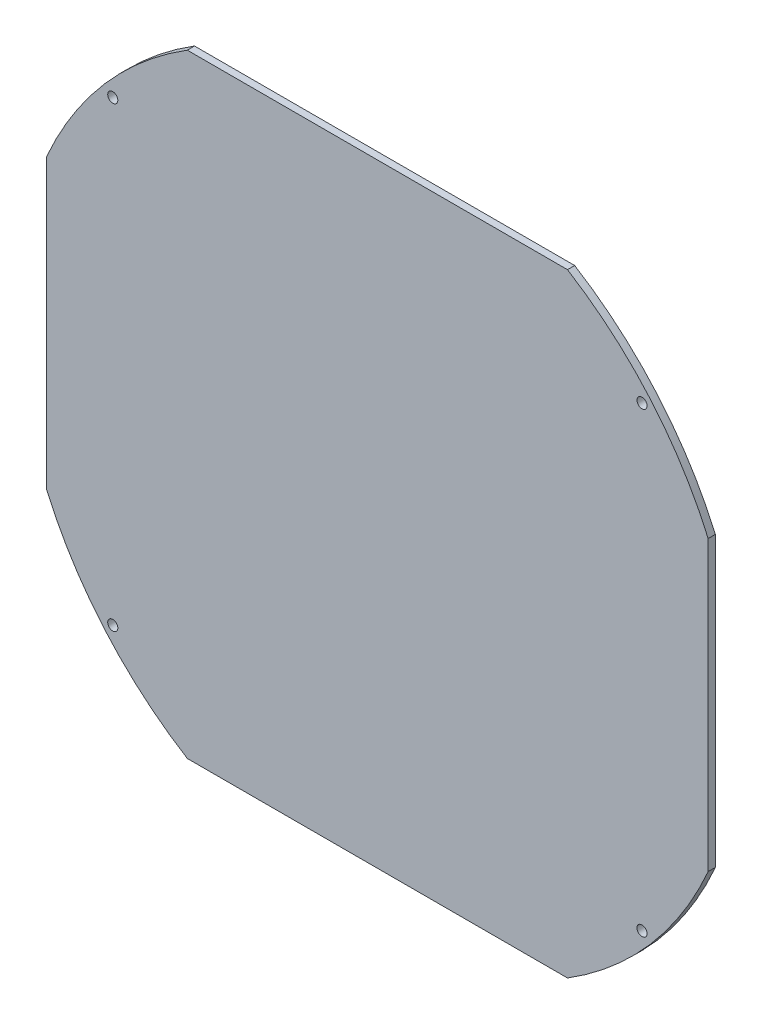
SolidWorks part; units mm, degrees
ref_plane "Front Plane" through (0, 0, 0) normal (0, 0, 1) x (1, 0, 0)
ref_plane "Top Plane" through (0, 0, 0) normal (0, 1, 0) x (1, 0, 0)
ref_plane "Right Plane" through (0, 0, 0) normal (1, 0, 0) x (0, 0, -1)
sketch "Sketch2" plane through (0, 0, 0) normal (0, 0, 1) x (1, 0, 0)
  line L0 (0, 0) -> (0, 125) construction
  line L1 (-57.1063, 125) -> (57.1063, 125)
  line L2 (136.8063, -13.0445) -> (79.7, -111.9555)
  line L3 (0, 0) -> (108.2532, -62.5) construction
  line L4 (-79.7, -111.9555) -> (-136.8063, -13.0445)
  line L5 (0, 0) -> (-108.2532, -62.5) construction
  arc A0 (-79.7, -111.9555) -> (79.7, -111.9555) centre (0, 125) ccw
  arc A1 (-57.1063, 125) -> (-136.8063, -13.0445) centre (108.2532, -62.5) ccw
  arc A2 (136.8063, -13.0445) -> (57.1063, 125) centre (-108.2532, -62.5) ccw
  point P20 (0, 0)
  dimension "D1" = 250
  dimension "D3" = 125
  dimension "D2" = 3
sketch "Sketch1" plane through (0, 0, 0) normal (0, 0, 1) x (1, 0, 0)
  line L0 (0, 0) -> (0, 125) construction
  line L1 (-100, -100) -> (100, -100)
  line L2 (-100, -100) -> (-100, 100)
  line L3 (-100, 100) -> (100, 100)
  line L4 (100, -100) -> (100, 100)
  line L5 (-100, -100) -> (100, 100) construction
  line L6 (-100, 100) -> (100, -100) construction
  line L7 (-79.0174, -127.5) -> (79.0174, -127.5)
  line L8 (-137.5, -59.9479) -> (-137.5, 59.9479)
  line L9 (-79.0174, 127.5) -> (79.0174, 127.5)
  line L10 (137.5, -59.9479) -> (137.5, 59.9479)
  line L11 (-106.066, -106.066) -> (106.066, 106.066) construction
  line L12 (-106.066, 106.066) -> (106.066, -106.066) construction
  line L13 (0, 71.7773) -> (0, 0) construction
  line L14 (0, 0) -> (57.5333, 0) construction
  circle A0 centre (0, 0) radius 125
  arc A1 (79.0174, -127.5) -> (137.5, -59.9479) centre (0, 0) ccw
  arc A2 (137.5, 59.9479) -> (79.0174, 127.5) centre (0, 0) ccw
  arc A3 (-79.0174, 127.5) -> (-137.5, 59.9479) centre (0, 0) ccw
  arc A4 (-137.5, -59.9479) -> (-79.0174, -127.5) centre (0, 0) ccw
  dimension "D1" = 200
  dimension "D3" = 275
  dimension "D4" = 300
  dimension "D2" = 250
  dimension "D5" = 255
extrude "Boss-Extrude1" add sketch "Sketch1" along normal blind 3 contours L9 A2 L10 A1 L7 A4 L8 A3
sketch "Sketch3" plane through (0, 0, 3) normal (0, 0, 1) x (1, 0, 0)
  line L0 (0, 45.3209) -> (0, 0) construction
  line L1 (0, 0) -> (45.3193, 0) construction
  circle A0 centre (-110, 95) radius 2.1
  circle A1 centre (110, 95) radius 2.1
  circle A2 centre (110, -95) radius 2.1
  circle A3 centre (-110, -95) radius 2.1
  dimension "D1" = 4.2
  dimension "D3" = 190
  dimension "D2" = 220
extrude "Cut-Extrude1" cut sketch "Sketch3" against normal through all
